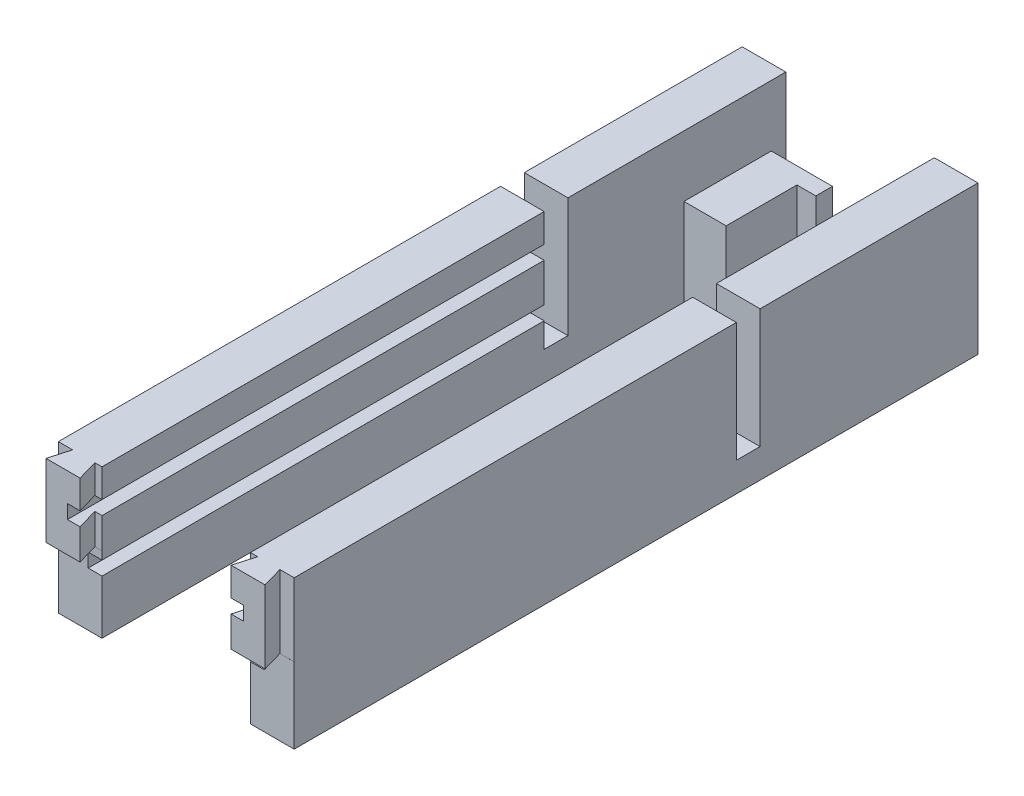
SolidWorks part; units mm, degrees
ref_plane "Front Plane" through (0, 0, 0) normal (0, 0, 1) x (1, 0, 0)
ref_plane "Top Plane" through (0, 0, 0) normal (0, 1, 0) x (1, 0, 0)
ref_plane "Right Plane" through (0, 0, 0) normal (1, 0, 0) x (0, 0, -1)
sketch "Sketch1" plane through (0, 0, 0) normal (1, 0, 0) x (0, 0, -1)
  line L1 (-64.5621, 30.5573) -> (177.4379, 30.5573)
  line L2 (-64.5621, 30.5573) -> (-64.5621, -20.4427)
  line L3 (-64.5621, -20.4427) -> (177.4379, -20.4427)
  line L4 (177.4379, 30.5573) -> (177.4379, -20.4427)
  dimension "D1" = 242
  dimension "D2" = 51
extrude "Boss-Extrude1" add sketch "Sketch1" along normal blind 15 contours L2 L3 L4 L1
sketch "Sketch26" plane through (0, 0, 0) normal (-1, 0, 0) x (0, 0, 1)
  line L1 (-172.4379, 9.5573) -> (-142.4379, 9.5573)
  line L2 (-172.4379, 9.5573) -> (-172.4379, -20.4427)
  line L3 (-172.4379, -20.4427) -> (-142.4379, -20.4427)
  line L4 (-142.4379, 9.5573) -> (-142.4379, -20.4427)
  line L5 (64.5621, -20.4427) -> (-177.4379, -20.4427) construction
  line L6 (-177.4379, 30.5573) -> (-177.4379, -20.4427) construction
  dimension "D1" = 5
  dimension "D2" = 30
  dimension "D3" = 30
extrude "Boss-Extrude3" add sketch "Sketch26" against normal blind 29.5
sketch "Sketch28" plane through (29.5, 0, 0) normal (1, 0, 0) x (0, 0, -1)
  line L0 (147.0417, -20.4427) -> (147.0417, -10.6927)
  line L1 (172.4379, -20.4427) -> (142.4379, -20.4427) construction
  line L2 (147.0417, -10.6927) -> (162.0417, -10.6927)
  line L3 (162.0417, -10.6927) -> (162.0417, -20.4427)
  line L4 (162.0417, -20.4427) -> (147.0417, -20.4427)
  dimension "D1" = 9.75
  dimension "D2" = 15
extrude "Boss-Extrude5" add sketch "Sketch28" along normal blind 4.5
sketch "Sketch29" plane through (29.5, 0, 0) normal (1, 0, 0) x (0, 0, -1)
  line L0 (172.4379, 9.5573) -> (166.7379, 9.5573)
  line L1 (142.4379, 9.5573) -> (172.4379, 9.5573) construction
  line L2 (166.7379, 9.5573) -> (166.7379, -10.4427)
  line L3 (166.7379, -10.4427) -> (172.4379, -10.4427)
  line L4 (172.4379, 9.5573) -> (172.4379, -20.4427) construction
  line L5 (172.4379, -10.4427) -> (172.4379, 9.5573)
  dimension "D1" = 20
  dimension "D2" = 5.7
extrude "Boss-Extrude6" add sketch "Sketch29" along normal blind 6.5
sketch "Sketch12" plane through (0, 30.5573, 0) normal (0, 1, 0) x (1, 0, 0)
  line L0 (0, -57.4487) -> (4.9097, -57.4487)
  line L1 (0, -64.5621) -> (0, 177.4379) construction
  line L2 (4.9097, -57.4487) -> (2.87, -64.5621)
  line L3 (15, -64.5621) -> (0, -64.5621) construction
  line L4 (2.87, -64.5621) -> (0, -64.5621)
  line L5 (0, -64.5621) -> (0, -57.4487)
  line L6 (15, -57.4487) -> (15, -64.5621)
  line L7 (15, -64.5621) -> (15, 177.4379) construction
  line L8 (15, -64.5621) -> (14.57, -64.5621)
  line L9 (14.57, -64.5621) -> (12.5303, -57.4487)
  line L10 (12.5303, -57.4487) -> (15, -57.4487)
  dimension "D1" = 7.4
  dimension "D2" = 7.4
  dimension "D3" = 106
  dimension "D4" = 106
  dimension "D5" = 11.7
  dimension "D6" = 2.87
extrude "Cut-Extrude8" cut sketch "Sketch12" against normal blind 25
sketch "Sketch13" plane through (0, -20.4427, 0) normal (0, -1, 0) x (1, 0, 0)
  line L0 (15, 64.5621) -> (15, -142.4379) construction
  line L1 (0, 64.5621) -> (15, 64.5621)
  line L2 (0, 64.5621) -> (0, 57.4521)
  line L3 (0, 57.4521) -> (15, 57.4521)
  line L4 (15, 64.5621) -> (15, 57.4521)
  dimension "D1" = 7.11
extrude "Cut-Extrude9" cut sketch "Sketch13" against normal blind 26
sketch "Sketch17" plane through (0, 30.5573, 0) normal (0, 1, 0) x (1, 0, 0)
  line L0 (15, -57.4487) -> (15, 177.4379) construction
  line L1 (0, 110.4379) -> (15, 110.4379)
  line L2 (0, 110.4379) -> (0, 102.5879)
  line L3 (0, 102.5879) -> (15, 102.5879)
  line L4 (15, 110.4379) -> (15, 102.5879)
  line L6 (0, 102.5879) -> (15, 102.5879)
  line L7 (0, 102.5879) -> (0, 94.4379)
  line L8 (0, 94.4379) -> (15, 94.4379)
  line L9 (15, 102.5879) -> (15, 94.4379)
  line M14 (15, -57.4487) -> (15, 177.4379)
  line M16 (0, 177.4379) -> (0, -57.4487)
  dimension "D1" = 7.85
  dimension "D2" = 8.15
extrude "Cut-Extrude10" cut sketch "Sketch17" against normal blind 41 contours L8 L3 M16 M14
sketch "Sketch7" plane through (0, 0, -94.4379) normal (0, 0, -1) x (-1, 0, 0)
  line L0 (-15, -20.4427) -> (-15, -1.9427)
  line L1 (-15, 2.8073) -> (-15, 16.0573)
  line L2 (-10.25, 2.8073) -> (-15, 2.8073)
  line L3 (-10.25, 2.8073) -> (-10.25, -1.9427)
  line L4 (-10.25, -1.9427) -> (-15, -1.9427)
  line L5 (-15, 2.8073) -> (-15, -1.9427)
  line L6 (-15, 30.5573) -> (-15, -20.4427) construction
  line L8 (-15, 16.0573) -> (-10.25, 16.0573)
  line L9 (-15, 16.0573) -> (-15, 20.8073)
  line L10 (-15, 20.8073) -> (-10.25, 20.8073)
  line L11 (-10.25, 16.0573) -> (-10.25, 20.8073)
  dimension "D1" = 18.5
  dimension "D2" = 4.75
  dimension "D3" = 4.75
  dimension "D4" = 13.25
  dimension "D5" = 4.75
  dimension "D6" = 4.75
extrude "Cut-Extrude5" cut sketch "Sketch7" against normal blind 165
sketch "Sketch22" plane through (0, 30.5573, 0) normal (0, 1, 0) x (1, 0, 0)
  line L0 (15, 177.4379) -> (15, 161.9379)
  line L1 (15, 102.5879) -> (15, 177.4379) construction
  line L3 (15, 161.9379) -> (8, 161.9379)
  line L4 (15, 161.9379) -> (15, 158.7879)
  line L5 (15, 158.7879) -> (8, 158.7879)
  line L6 (8, 161.9379) -> (8, 158.7879)
  line M5 (15, 102.5879) -> (15, 177.4379)
  dimension "D1" = 15.5
  dimension "D2" = 7
  dimension "D3" = 3.15
extrude "Cut-Extrude13" [suppressed] cut sketch "Sketch22" against normal blind 45 contours L3 L6 L5 M5
ref_plane "Plane1" through (40.5, 0, 0) normal (1, 0, 0) x (0, 0, -1)
sketch "Sketch18" [suppressed] plane through (0, 30.5573, 0) normal (0, 1, 0) x (1, 0, 0)
  line L0 (15, 102.5879) -> (15, 136.5879)
  line L1 (15, 102.5879) -> (15, 177.4379) construction
  line L3 (15, 136.5879) -> (10, 136.5879)
  line L4 (15, 136.5879) -> (15, 144.0879)
  line L5 (15, 144.0879) -> (10, 144.0879)
  line L6 (10, 136.5879) -> (10, 144.0879)
  line M6 (15, 102.5879) -> (15, 177.4379)
  dimension "D1" = 34
  dimension "D2" = 5
  dimension "D3" = 7.5
extrude "Cut-Extrude11" [suppressed] cut sketch "Sketch18" against normal blind 38 contours L6 L3 L5 M6
sketch "Sketch23" [suppressed] plane through (0, 0, -177.4379) normal (0, 0, -1) x (-1, 0, 0)
  line L0 (-15, -20.4427) -> (-15, 9.0573)
  line L1 (-15, 30.5573) -> (-15, -20.4427) construction
  line L3 (-15, 9.0573) -> (-10.5, 9.0573)
  line L4 (-15, 9.0573) -> (-15, 13.5573)
  line L5 (-15, 13.5573) -> (-10.5, 13.5573)
  line L6 (-10.5, 9.0573) -> (-10.5, 13.5573)
  line M5 (-15, 30.5573) -> (-15, -20.4427)
  dimension "D1" = 4.5
  dimension "D2" = 4.5
  dimension "D3" = 29.5
extrude "Cut-Extrude14" [suppressed] cut sketch "Sketch23" against normal blind 45 contours L3 L6 L5 M5
mirror "Mirror4" about plane through (40.5, 0, 0) normal (1, 0, 0) of bodies 107 113
